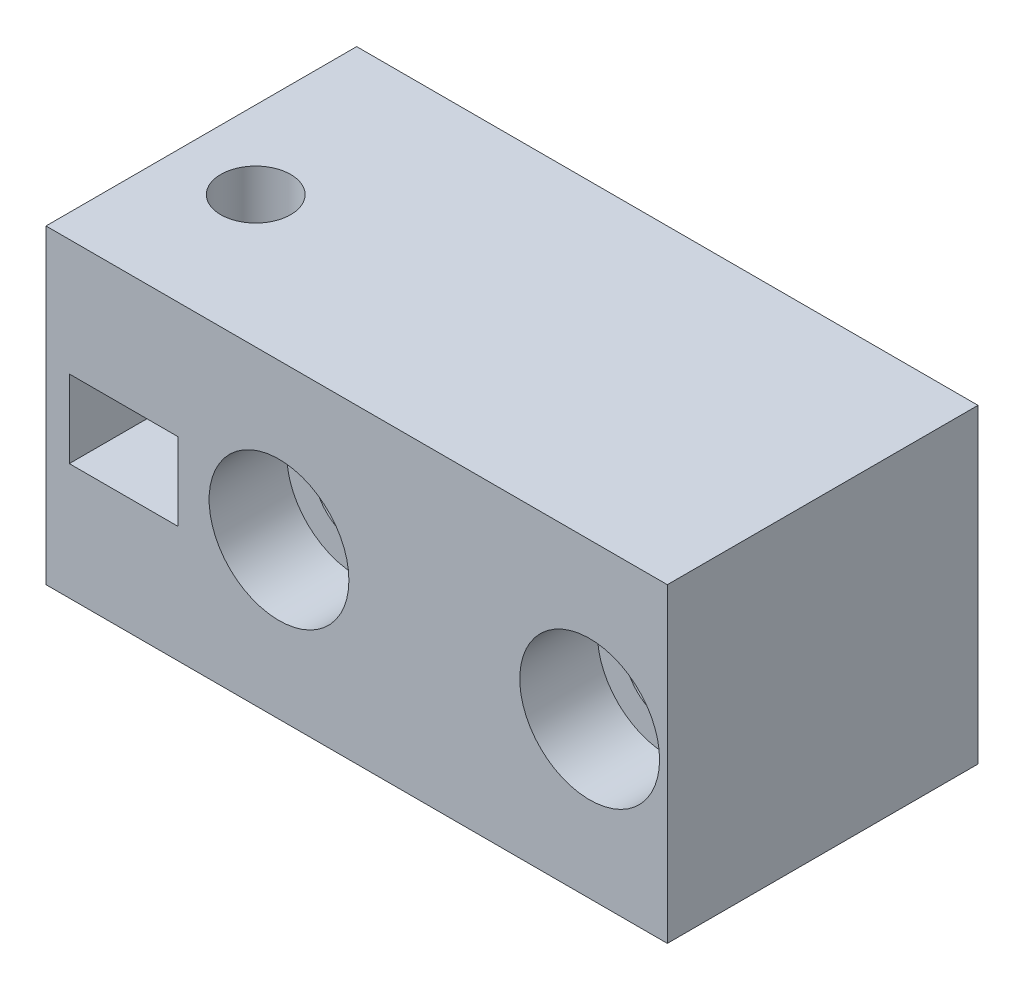
SolidWorks part; units mm, degrees
ref_plane "Front Plane" through (0, 0, 0) normal (0, 0, 1) x (1, 0, 0)
ref_plane "Top Plane" through (0, 0, 0) normal (0, 1, 0) x (1, 0, 0)
ref_plane "Right Plane" through (0, 0, 0) normal (1, 0, 0) x (0, 0, -1)
sketch "Sketch1" plane through (0, 0, 0) normal (0, 0, 1) x (1, 0, 0)
  line L1 (0, 0) -> (50, 0)
  line L2 (0, 0) -> (0, 20)
  line L3 (0, 20) -> (50, 20)
  line L4 (50, 0) -> (50, 20)
  dimension "D1" = 20
  dimension "D2" = 50
extrude "Boss-Extrude1" add sketch "Sketch1" along normal blind 20
sketch "Sketch2" plane through (0, 0, 20) normal (0, 0, 1) x (1, 0, 0)
  line L0 (50, 20) -> (0, 20) construction
  line L1 (0, 20) -> (0, 0) construction
  line L2 (50, 0) -> (50, 20) construction
  line L4 (11.5, 7.5) -> (18.5, 7.5)
  line L5 (11.5, 7.5) -> (11.5, 12.5)
  line L6 (11.5, 12.5) -> (18.5, 12.5)
  line L7 (18.5, 7.5) -> (18.5, 12.5)
  circle A0 centre (25, 10) radius 2.75
  circle A1 centre (45, 10) radius 2.75
  dimension "D1" = 5.5
  dimension "D2" = 5.5
  dimension "D3" = 10
  dimension "D4" = 10
  dimension "D5" = 25
  dimension "D6" = 5
  dimension "D7" = 5
  dimension "D8" = 7
  dimension "D9" = 11.5
  dimension "D10" = 7.5
extrude "Cut-Extrude1" cut sketch "Sketch2" against normal through all
sketch "Sketch3" plane through (0, 20, 0) normal (0, 1, 0) x (1, 0, 0)
  line L0 (0, -20) -> (0, 0) construction
  line L1 (50, 0) -> (0, 0) construction
  circle A0 centre (15, -11.5) radius 2.25
  dimension "D1" = 4.5
  dimension "D2" = 15
  dimension "D3" = 11.5
extrude "Cut-Extrude2" cut sketch "Sketch3" against normal through all
sketch "Sketch5" plane through (0, 0, 0) normal (0, 0, -1) x (-1, 0, 0)
  line L0 (-50, 20) -> (0, 20) construction
  line L1 (-39, 7) -> (-31, 7)
  line L2 (-39, 7) -> (-39, 13)
  line L3 (-39, 13) -> (-31, 13)
  line L4 (-31, 7) -> (-31, 13)
  line L5 (-50, 0) -> (-50, 20) construction
  dimension "D1" = 6
  dimension "D2" = 8
  dimension "D3" = 7
  dimension "D4" = 11
extrude "Boss-Extrude3" add sketch "Sketch5" along normal blind 3
sketch "Sketch6" plane through (0, 0, 20) normal (0, 0, 1) x (1, 0, 0)
  circle A0 centre (25, 10) radius 4.5
  circle A1 centre (45, 10) radius 4.5
  dimension "D1" = 9
  dimension "D2" = 9
extrude "Cut-Extrude3" cut sketch "Sketch6" against normal blind 5
sketch "Sketch7" plane through (0, 0, 20) normal (0, 0, 1) x (1, 0, 0)
  line L0 (0, 0) -> (50, 0) construction
  line L1 (0, 20) -> (10, 20)
  line L2 (0, 20) -> (0, 0)
  line L3 (0, 0) -> (10, 0)
  line L4 (10, 20) -> (10, 0)
  dimension "D1" = 10
extrude "Cut-Extrude4" cut sketch "Sketch7" against normal through all
